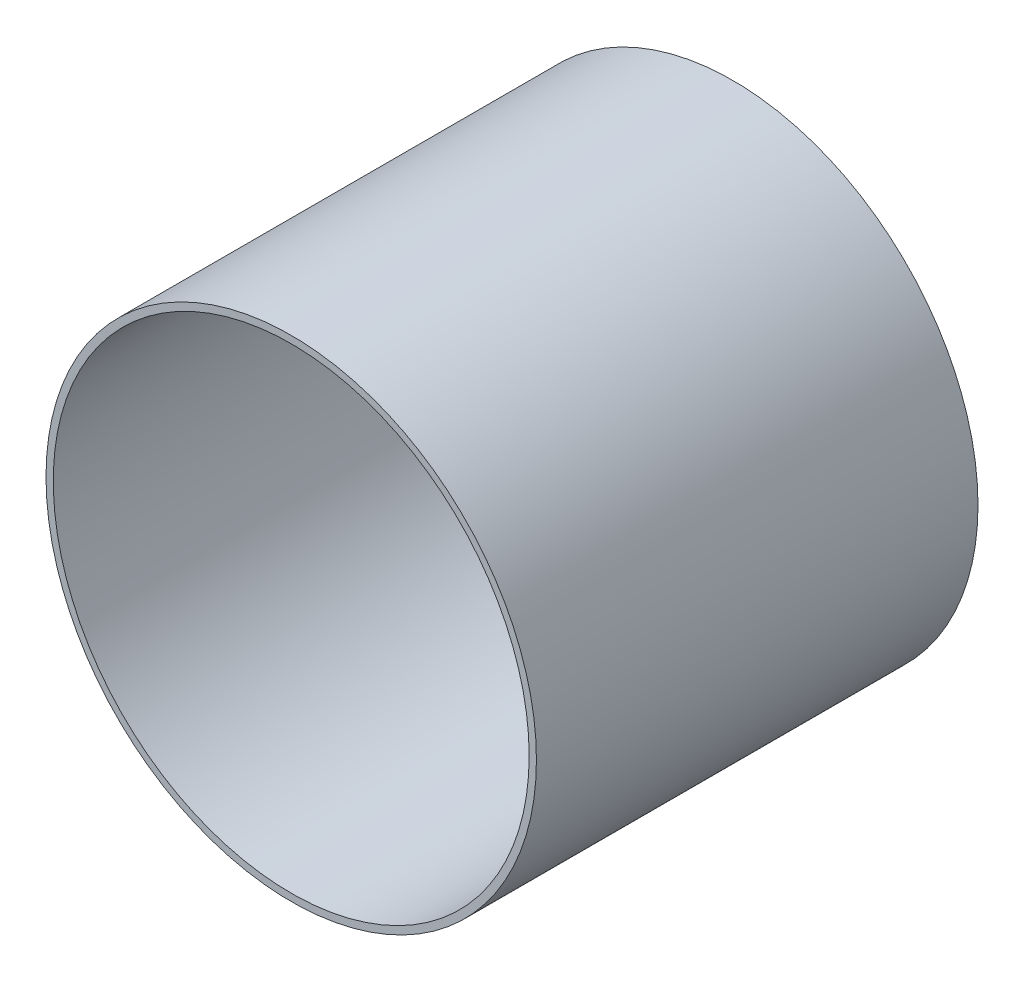
SolidWorks part; units mm, degrees
ref_plane "Front Plane" through (0, 0, 0) normal (0, 0, 1) x (1, 0, 0)
ref_plane "Top Plane" through (0, 0, 0) normal (0, 1, 0) x (1, 0, 0)
ref_plane "Right Plane" through (0, 0, 0) normal (1, 0, 0) x (0, 0, -1)
sketch "Sketch1" plane through (0, 0, 0) normal (0, 0, 1) x (1, 0, 0)
  circle A0 centre (0, 0) radius 63.4746
  circle A1 centre (0, 0) radius 61.595
  dimension "D1" = 123.19
  dimension "D2" = 126.9492
extrude "Boss-Extrude1" add sketch "Sketch1" along normal mid plane 114.3
equation "\"AIRFRAME_OD\"= 5.15in"
equation "\"AIRFRAME_ID\"= 4.99in"
equation "\"FLAT_T\"= 0.125in"
equation "\"NOSE_EXP_L\"= 27in"
equation "\"NOSE_SHOULDER_L\"= 5in"
equation "\"MAIN_L\"= 30in"
equation "\"RECO_COUP_L\"= 10in"
equation "\"RECO_SWITCH_L\"= 2in"
equation "\"DROGUE_L\"= 20in"
equation "\"ATS_FORE_COUP_L\"= 5.5in"
equation "\"ATS_AFT_COUP_L\"= 4.5in"
equation "\"LOWER_L\"= 30in"
equation "\"FIN_N\"= 4"
equation "\"CR_AFT_X\"= 0.5in"
equation "\"CR_FORE_X\"= 9.25in"
equation "\"D1@Sketch1\"=\"COUPLER_ID\""
equation "\"D2@Sketch1\"=\"COUPLER_OD\""
equation "\"D1@Boss-Extrude1\"=\"ATS_AFT_COUP_L\""
equation "\"FIN_ROOT\"= 8in"
equation "\"FIN_X\"= 0.75in"
equation "\"MOTOR_OD\"= 3.091in"
equation "\"MOTOR_ID\"= 3.00in"
equation "\"COUPLER_OD\"= 4.998in"
equation "\"COUPLER_ID\"= 4.85in"
equation "\"RECO_ROD_X\"= 3.5in"
equation "\"ATS_ROD_X\"= 3.75in"
equation "\"MOTOR_L\"= 14in"
equation "\"MOTOR_LOWER_X\"= 2in"
